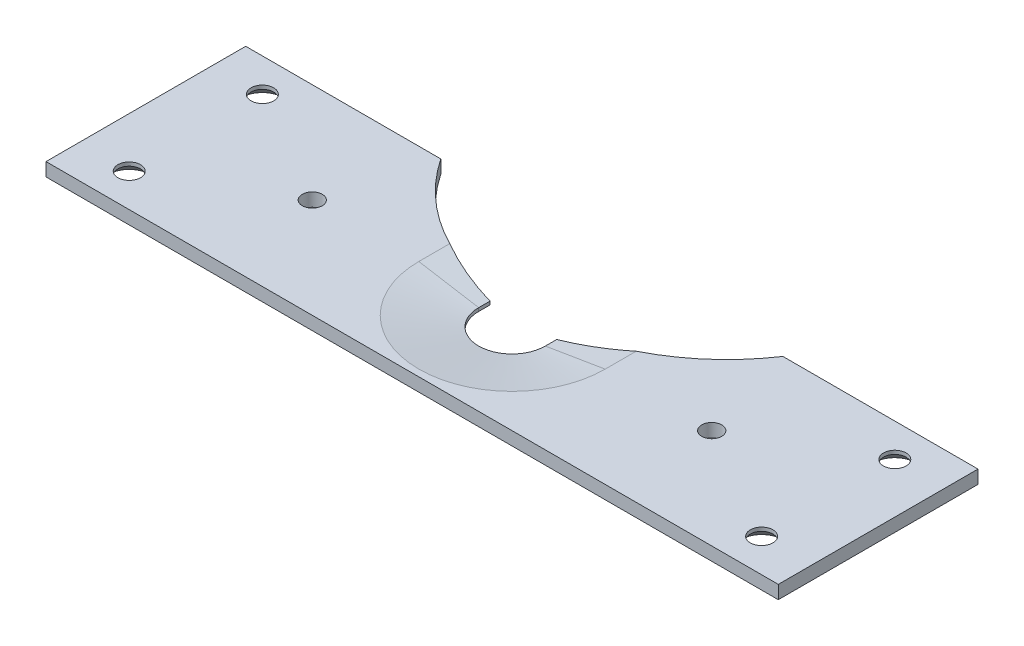
SolidWorks part; units mm, degrees
ref_plane "Front Plane" through (0, 0, 0) normal (0, 0, 1) x (1, 0, 0)
ref_plane "Top Plane" through (0, 0, 0) normal (0, 1, 0) x (1, 0, 0)
ref_plane "Right Plane" through (0, 0, 0) normal (1, 0, 0) x (0, 0, -1)
sketch "Sketch1" plane through (0, 0, 0) normal (0, 1, 0) x (1, 0, 0)
  line L1 (-55, 15) -> (55, 15)
  line L2 (-55, 15) -> (-55, -15)
  line L3 (-55, -15) -> (55, -15)
  line L4 (55, 15) -> (55, -15)
  dimension "D5" = 15
  dimension "D1" = 55
  dimension "D2" = 55
  dimension "D4" = 15
extrude "Extrude1" add sketch "Sketch1" along normal blind 2
sketch "Sketch2" plane through (0, 2, 0) normal (0, 1, 0) x (-1, 0, 0)
  line L0 (-55, -15) -> (55, -15) construction
  line L2 (5, 0) -> (5, -15)
  line L3 (5, -15) -> (-5, -15)
  line L4 (-5, 0) -> (-5, -15)
  arc A1 (5, 0) -> (-5, 0) centre (0, 0) ccw
extrude "Cut-Extrude1" cut sketch "Sketch2" against normal through all
chamfer "Chamfer1" distance 9 distance2 1.5 3 edges at (5, 2, -7.5) (0, 2, 5) (-5, 2, -7.5)
hole_wizard "CSK for M3 Countersunk Raised Head Screw1" positions "Sketch9" profile "Sketch8" countersink size "M3" standard "ISO" end condition through all
sketch "Sketch9" plane through (0, 0, 0) normal (0, -1, 0) x (1, 0, 0)
  line L0 (-55, -15) -> (-55, 15) construction
  line L1 (55, 15) -> (55, -15) construction
  line L3 (-55, 15) -> (55, 15) construction
  line L4 (55, -15) -> (5, -15) construction
  point P0 (47.5, -10)
  point P1 (-47.5, -10)
  point P4 (-47.5, 10)
  point P6 (47.5, 10)
  dimension "D1" = 7.5
  dimension "D2" = 7.5
  dimension "D3" = 5
  dimension "D4" = 5
sketch "Sketch8" plane through (47.5, 0, -10) normal (1, 0, 0) x (0, 0, -1)
  line L0 (0, 0) -> (0, 2)
  line L1 (0, 2) -> (1.7, 2)
  line L2 (1.7, 2) -> (1.7, 1.45)
  line L3 (1.7, 1.45) -> (3.15, 0)
  line L5 (3.15, 0) -> (0, 0)
  line L6 (-1.7, 1.45) -> (-3.15, 0) construction
  line L11 (0, -6.35) -> (0, 107.95) construction
  dimension "Thru Hole Dia." = 3.4
  dimension "Thru Hole Depth" = 2
  dimension "Near C'Sink Dia." = 6.3
  dimension "Near C'Sink Angle" = 90
hole_wizard "M3 Tapped Hole1" positions "Sketch11" profile "Sketch12" tap size "M3" standard "ISO" end condition through all
sketch "Sketch11" plane through (0, 2, 0) normal (0, 1, 0) x (-1, 0, 0)
  line L0 (55, 15) -> (-55, 15) construction
  line L1 (-55, 15) -> (-55, -15) construction
  line L2 (55, -15) -> (55, 15) construction
  point P5 (-30, 0)
  point P7 (30, 0)
  dimension "D1" = 15
  dimension "D2" = 25
  dimension "D3" = 25
sketch "Sketch12" plane through (30, 2, 0) normal (1, 0, 0) x (0, 0, 1)
  line L0 (0, 0) -> (0, 2)
  line L1 (0, 2) -> (1.5, 2)
  line L2 (1.5, 2) -> (1.5, 0)
  line L5 (1.5, 0) -> (0, 0)
  line L11 (0, -6.35) -> (0, 107.95) construction
  dimension "Thread Major Dia." = 3
  dimension "Thru Tap Drill Depth" = 2
sketch "Sketch13" plane through (0, 0, 0) normal (0, -1, 0) x (1, 0, 0)
  circle A0 centre (0, -32.271) radius 30.9632
extrude "Cut-Extrude2" cut sketch "Sketch13" against normal through all
equation "\"D2@Sketch1\" = \"D1@Sketch1\""
equation "\"D5@Sketch1\"=\"D4@Sketch1\""
equation "\"D2@Sketch9\" = \"D1@Sketch9\""
equation "\"D4@Sketch9\" = \"D3@Sketch9\""
equation "\"D3@Sketch11\" = \"D2@Sketch11\""
